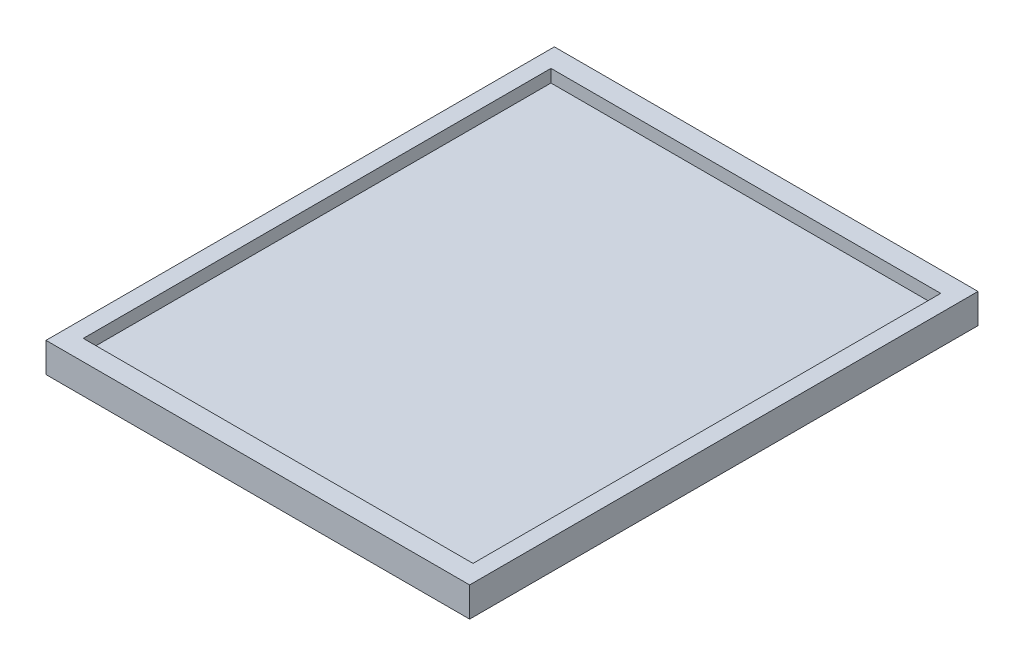
SolidWorks part; units mm, degrees
ref_plane "Plano frontal" through (0, 0, 0) normal (0, 0, 1) x (1, 0, 0)
ref_plane "Plano superior" through (0, 0, 0) normal (0, 1, 0) x (1, 0, 0)
ref_plane "Plano direito" through (0, 0, 0) normal (1, 0, 0) x (0, 0, -1)
sketch "Esboço1" plane through (0, 0, 0) normal (0, 1, 0) x (1, 0, 0)
  line L1 (0, 0) -> (100, 0)
  line L2 (0, 0) -> (0, 120)
  line L3 (0, 120) -> (100, 120)
  line L4 (100, 0) -> (100, 120)
  dimension "D1" = 100
  dimension "D2" = 120
extrude "Ressalto-extrusão1" add sketch "Esboço1" along normal blind 4
sketch "Esboço3" plane through (0, 0, 0) normal (0, 1, 0) x (1, 0, 0)
  line L0 (0, 120) -> (100, 0) construction
  line L1 (0, 120) -> (100, 120)
  line L2 (0, 120) -> (0, 0)
  line L3 (0, 0) -> (100, 0)
  line L4 (100, 120) -> (100, 0)
  line L6 (4, 115.2) -> (96, 115.2)
  line L7 (4, 115.2) -> (4, 4.8)
  line L8 (4, 4.8) -> (96, 4.8)
  line L9 (96, 115.2) -> (96, 4.8)
  dimension "D1" = 4
  dimension "D2" = 4
extrude "Ressalto-extrusão2" add sketch "Esboço3" along normal blind 7
